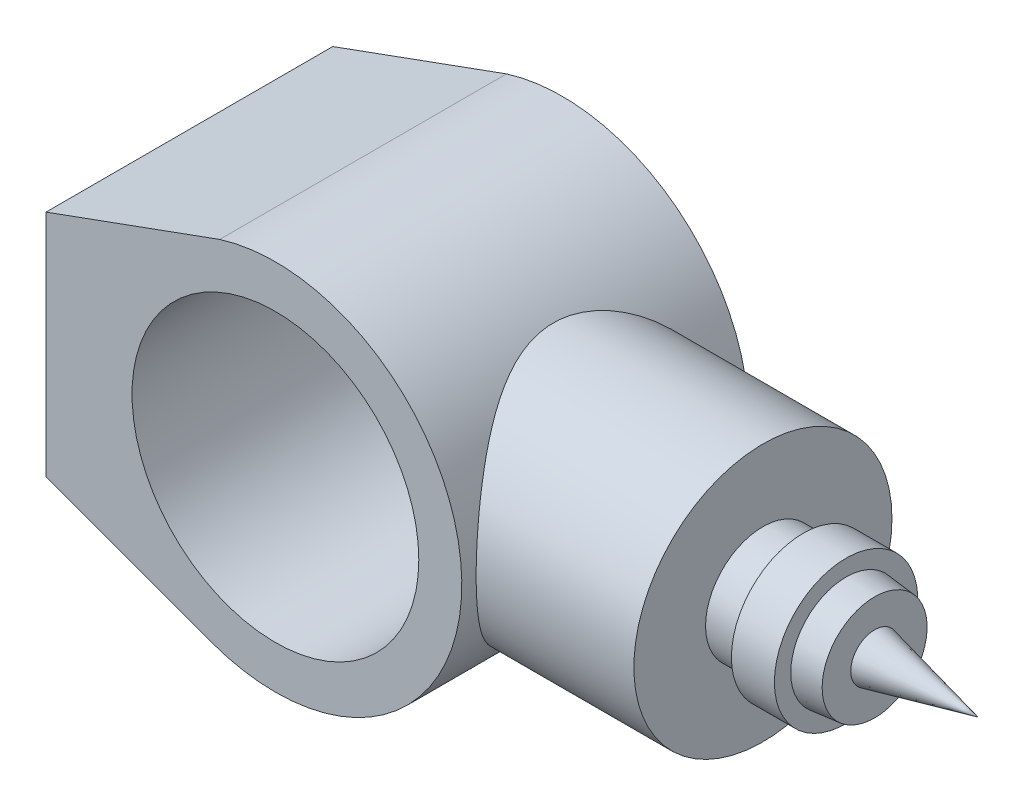
SolidWorks part; units mm, degrees
ref_plane "Front Plane" through (0, 0, 0) normal (0, 0, 1) x (1, 0, 0)
ref_plane "Top Plane" through (0, 0, 0) normal (0, 1, 0) x (1, 0, 0)
ref_plane "Right Plane" through (0, 0, 0) normal (1, 0, 0) x (0, 0, -1)
sketch "Sketch1" plane through (0, 0, 0) normal (0, 0, 1) x (1, 0, 0)
  line L0 (-80, -40) -> (-80, 40)
  line L1 (-80, 40) -> (-19.4213, 62.0308)
  line L2 (-80, -40) -> (-22.2817, -61.0617)
  arc A0 (-22.2817, -61.0617) -> (-19.4213, 62.0308) centre (0, 0) ccw
  circle A1 centre (0, 0) radius 50
  point P7 (-80, 0)
  dimension "D1" = 130
  dimension "D2" = 100
  dimension "D3" = 80
  dimension "D4" = 80
extrude "Boss-Extrude1" add sketch "Sketch1" along normal mid plane 100
ref_plane "Plane1" through (120, 0, 0) normal (1, 0, 0) x (0, 0, -1)
sketch "Sketch2" plane through (120, 0, 0) normal (1, 0, 0) x (0, 0, -1)
  circle A0 centre (0, 0) radius 45
  dimension "D1" = 90
extrude "Boss-Extrude2" add sketch "Sketch2" against normal up to next
sketch "Sketch3" plane through (0, 0, 0) normal (0, 0, 1) x (1, 0, 0)
  line L0 (0, 0) -> (266.1263, 0) construction
  line L1 (120, 0) -> (120, -20)
  line L3 (120, -45) -> (120, 45) construction
  line L4 (120, -20) -> (134, -20)
  line L5 (134, -20) -> (134, -25)
  line L6 (134, -25) -> (149, -25)
  line L7 (149, -25) -> (149, -19.2983)
  line L8 (149, -19.2983) -> (158.9502, -18.3013)
  line L9 (158.9502, -18.3013) -> (158.9502, -8.3313)
  line L10 (158.9502, -8.3313) -> (195, 0)
  line L11 (195, 0) -> (120, 0)
  dimension "D1" = 20
  dimension "D2" = 14
  dimension "D3" = 5
  dimension "D4" = 15
  dimension "D5" = 10
  dimension "D6" = 37
  dimension "D7" = 75
revolve "Revolve1" add sketch "Sketch3" angle 360 about L0
